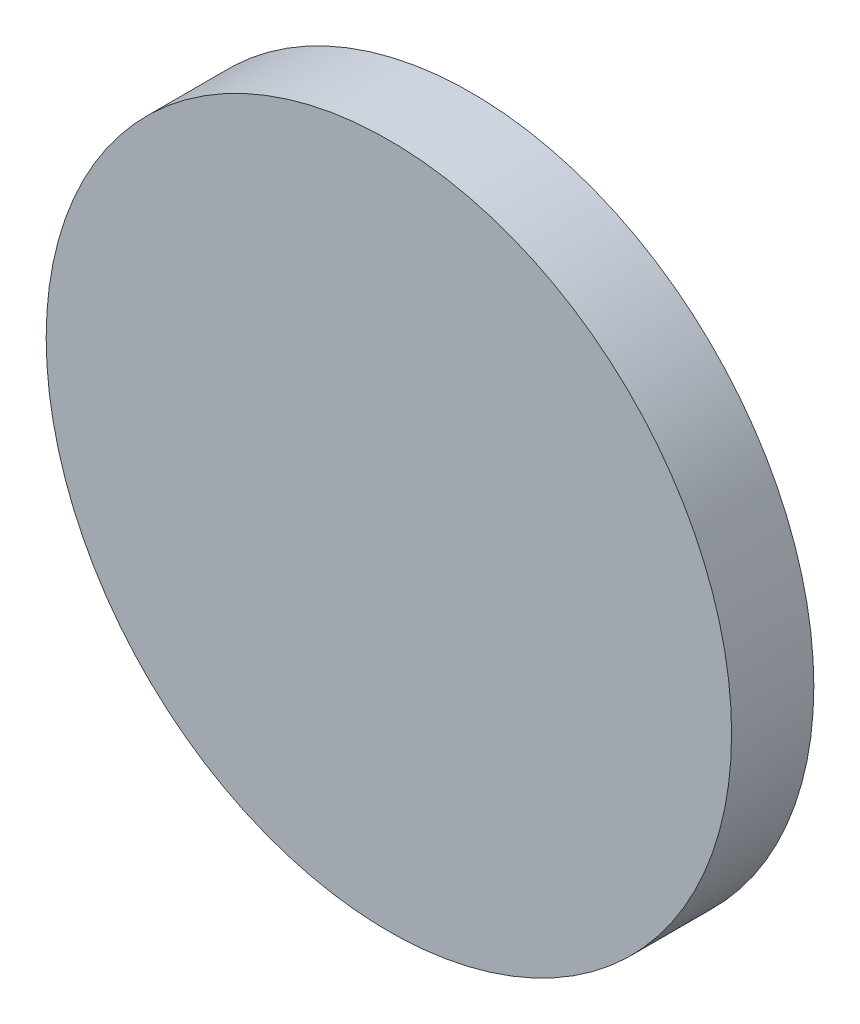
SolidWorks part; units mm, degrees
ref_plane "Front Plane" through (0, 0, 0) normal (0, 0, 1) x (1, 0, 0)
ref_plane "Top Plane" through (0, 0, 0) normal (0, 1, 0) x (1, 0, 0)
ref_plane "Right Plane" through (0, 0, 0) normal (1, 0, 0) x (0, 0, -1)
sketch "Sketch1" plane through (0, 0, 0) normal (0, 0, 1) x (1, 0, 0)
  circle A0 centre (0, 0) radius 31.75
extrude "Boss-Extrude1" add sketch "Sketch1" along normal blind 7.62
